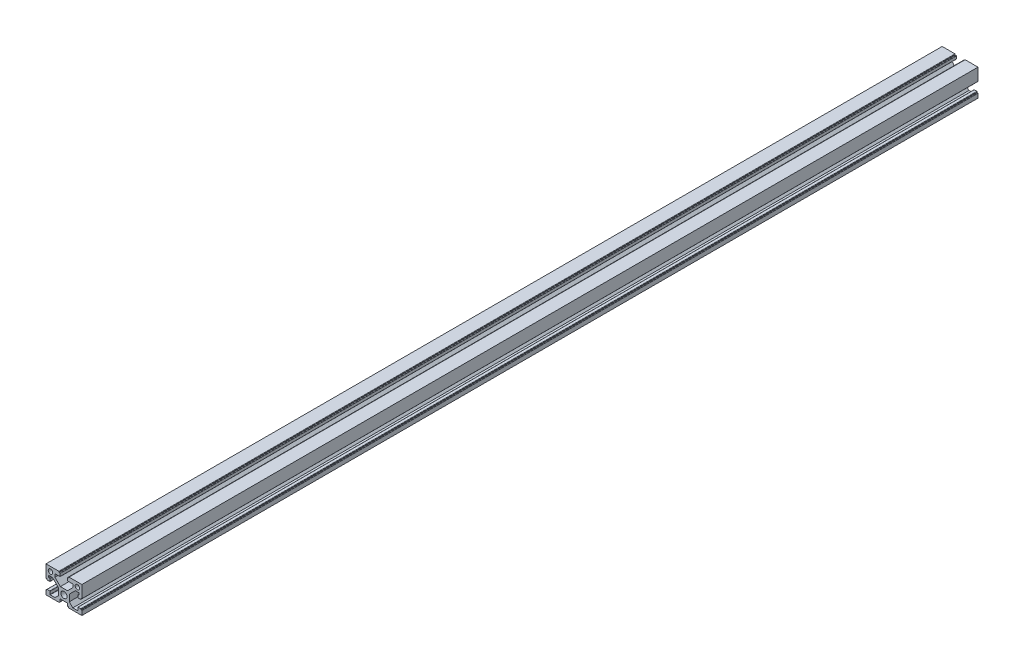
SolidWorks part; units mm, degrees
material "6063 T5"
ref_plane "Спереди" through (0, 0, 0) normal (0, 0, 1) x (1, 0, 0)
ref_plane "Сверху" through (0, 0, 0) normal (0, 1, 0) x (1, 0, 0)
ref_plane "Справа" through (0, 0, 0) normal (1, 0, 0) x (0, 0, -1)
sketch "Эскиз1" plane through (0, 0, 0) normal (0, 0, 1) x (1, 0, 0)
  line L0 (-20.0246, 21.0976) -> (19.9754, 21.0976) construction
  line L1 (-10, 20) -> (-20, 20)
  line L2 (-20, 20) -> (-20, 6.3)
  line L3 (-19.7, 6) -> (-19, 6)
  line L4 (-19, 6) -> (-19, 5.3)
  line L5 (-18.7, 5) -> (-15.8, 5)
  line L6 (-15.5, 5.3) -> (-15.5, 8)
  line L7 (-15.5, 8) -> (-16.7, 8)
  line L8 (-17, 8.3) -> (-17, 10.1)
  line L9 (-16.7, 10.4) -> (-12.7, 10.4)
  line L10 (-12.7, 10.4) -> (-6, 3.7)
  line L11 (-6, 3.7) -> (-6, -3.7)
  line L12 (-6, -3.7) -> (-9.9, -7.6)
  line L13 (-9.9, -7.6) -> (-15.2, -7.6)
  line L14 (-15.5, -7.3) -> (-15.5, -4.3)
  line L15 (-15.8, -4) -> (-18.7, -4)
  line L16 (-19, -4.3) -> (-19, -5)
  line L17 (-19, -5) -> (-19.7, -5)
  line L18 (-20, -5.3) -> (-20, -10)
  line L19 (-20, -10) -> (-5.4, -10)
  line L20 (-5.1, -9.7) -> (-5.1, -9)
  line L21 (-5.1, -9) -> (-4.4, -9)
  line L22 (-4.1, -8.7) -> (-4.1, -6)
  line L23 (-4.1, -6) -> (4.1, -6)
  line L24 (0, -6) -> (0, 0) construction
  line L25 (-15.5, 5) -> (-15.5, -4) construction
  line L26 (15.5, 5) -> (15.5, -4) construction
  line L27 (4.1, -8.7) -> (4.1, -6)
  line L28 (5.1, -9) -> (4.4, -9)
  line L29 (5.1, -9.7) -> (5.1, -9)
  line L30 (20, -10) -> (5.4, -10)
  line L31 (20, -5.3) -> (20, -10)
  line L32 (19, -5) -> (19.7, -5)
  line L33 (19, -4.3) -> (19, -5)
  line L34 (15.8, -4) -> (18.7, -4)
  line L35 (15.5, -7.3) -> (15.5, -4.3)
  line L36 (9.9, -7.6) -> (15.2, -7.6)
  line L37 (6, -3.7) -> (9.9, -7.6)
  line L38 (6, 3.7) -> (6, -3.7)
  line L39 (12.7, 10.4) -> (6, 3.7)
  line L40 (16.7, 10.4) -> (12.7, 10.4)
  line L41 (17, 8.3) -> (17, 10.1)
  line L42 (15.5, 8) -> (16.7, 8)
  line L43 (15.5, 5.3) -> (15.5, 8)
  line L44 (18.7, 5) -> (15.8, 5)
  line L45 (19, 6) -> (19, 5.3)
  line L46 (19.7, 6) -> (19, 6)
  line L47 (20, 20) -> (20, 6.3)
  line L48 (10, 20) -> (20, 20)
  line L49 (-15, 15) -> (15, 15) construction
  circle A0 centre (0, 0) radius 3.4
  arc A1 (-15.2, -7.6) -> (-15.5, -7.3) centre (-15.2, -7.3) cw
  arc A2 (-15.5, -4.3) -> (-15.8, -4) centre (-15.8, -4.3) ccw
  arc A3 (-18.7, -4) -> (-19, -4.3) centre (-18.7, -4.3) ccw
  arc A4 (-19.7, -5) -> (-20, -5.3) centre (-19.7, -5.3) ccw
  arc A5 (-20, 6.3) -> (-19.7, 6) centre (-19.7, 6.3) ccw
  arc A6 (-19, 5.3) -> (-18.7, 5) centre (-18.7, 5.3) ccw
  arc A7 (-15.8, 5) -> (-15.5, 5.3) centre (-15.8, 5.3) ccw
  arc A8 (-16.7, 8) -> (-17, 8.3) centre (-16.7, 8.3) cw
  arc A9 (-17, 10.1) -> (-16.7, 10.4) centre (-16.7, 10.1) cw
  arc A10 (17, 10.1) -> (16.7, 10.4) centre (16.7, 10.1) ccw
  arc A11 (16.7, 8) -> (17, 8.3) centre (16.7, 8.3) ccw
  arc A12 (15.8, 5) -> (15.5, 5.3) centre (15.8, 5.3) cw
  arc A13 (19, 5.3) -> (18.7, 5) centre (18.7, 5.3) cw
  arc A14 (20, 6.3) -> (19.7, 6) centre (19.7, 6.3) cw
  arc A15 (19.7, -5) -> (20, -5.3) centre (19.7, -5.3) cw
  arc A16 (18.7, -4) -> (19, -4.3) centre (18.7, -4.3) cw
  arc A17 (15.5, -4.3) -> (15.8, -4) centre (15.8, -4.3) cw
  arc A18 (15.2, -7.6) -> (15.5, -7.3) centre (15.2, -7.3) ccw
  arc A19 (5.1, -9.7) -> (5.4, -10) centre (5.4, -9.7) ccw
  arc A20 (4.1, -8.7) -> (4.4, -9) centre (4.4, -8.7) ccw
  arc A21 (-4.4, -9) -> (-4.1, -8.7) centre (-4.4, -8.7) ccw
  arc A22 (-5.4, -10) -> (-5.1, -9.7) centre (-5.4, -9.7) ccw
  circle A23 centre (15, 15) radius 2.5
  circle A24 centre (-15, 15) radius 2.5
  point P32 (0, 15)
  point P35 (-6, 0)
  point P45 (-20, -5)
  point P48 (-20, 6)
  point P57 (-17, 8)
  point P103 (17, 8)
  point P104 (20, 6)
  point P105 (20, -5)
  point P108 (5.1, -10)
  point P111 (4.1, -9)
  point P114 (-4.1, -9)
  point P117 (-5.1, -10)
  line B0 (10, 20) -> (5.7, 20)
  line B1 (5.4, 19.7) -> (5.4, 19)
  line B2 (5.4, 19) -> (4.4, 19)
  line B3 (4.1, 18.7) -> (4.1, 15.8)
  line B4 (4.4, 15.5) -> (9.7, 15.5)
  line B5 (10, 15.2) -> (10, 12)
  line B6 (10, 12) -> (4, 6)
  line B7 (0, 6) -> (0, 20) construction
  line B8 (-4, 6) -> (4, 6)
  line B9 (-10, 12) -> (-4, 6)
  line B10 (-10, 15.2) -> (-10, 12)
  line B11 (-4.4, 15.5) -> (-9.7, 15.5)
  line B12 (-4.1, 18.7) -> (-4.1, 15.8)
  line B13 (-5.4, 19) -> (-4.4, 19)
  line B14 (-5.4, 19.7) -> (-5.4, 19)
  line B15 (-10, 20) -> (-5.7, 20)
  arc B16 (9.7, 15.5) -> (10, 15.2) centre (9.7, 15.2) cw
  arc B17 (4.1, 15.8) -> (4.4, 15.5) centre (4.4, 15.8) ccw
  arc B18 (4.4, 19) -> (4.1, 18.7) centre (4.4, 18.7) ccw
  arc B19 (5.7, 20) -> (5.4, 19.7) centre (5.7, 19.7) ccw
  arc B20 (-5.7, 20) -> (-5.4, 19.7) centre (-5.7, 19.7) cw
  arc B21 (-4.4, 19) -> (-4.1, 18.7) centre (-4.4, 18.7) cw
  arc B22 (-4.1, 15.8) -> (-4.4, 15.5) centre (-4.4, 15.8) cw
  arc B23 (-9.7, 15.5) -> (-10, 15.2) centre (-9.7, 15.2) ccw
  line B24 (-10, 20) -> (-5.7, 20)
  line B25 (-5.4, 19.7) -> (-5.4, 19)
  line B26 (-5.4, 19) -> (-4.4, 19)
  line B27 (-4.1, 18.7) -> (-4.1, 15.8)
  line B28 (-4.4, 15.5) -> (-9.7, 15.5)
  line B29 (-10, 15.2) -> (-10, 12)
  line B30 (-10, 12) -> (-4, 6)
  line B31 (0, 6) -> (0, 20) construction
  line B32 (4, 6) -> (-4, 6)
  line B33 (10, 12) -> (4, 6)
  line B34 (10, 15.2) -> (10, 12)
  line B35 (4.4, 15.5) -> (9.7, 15.5)
  line B36 (4.1, 18.7) -> (4.1, 15.8)
  line B37 (5.4, 19) -> (4.4, 19)
  line B38 (5.4, 19.7) -> (5.4, 19)
  line B39 (10, 20) -> (5.7, 20)
  arc B40 (-9.7, 15.5) -> (-10, 15.2) centre (-9.7, 15.2) ccw
  arc B41 (-4.1, 15.8) -> (-4.4, 15.5) centre (-4.4, 15.8) cw
  arc B42 (-4.4, 19) -> (-4.1, 18.7) centre (-4.4, 18.7) cw
  arc B43 (-5.7, 20) -> (-5.4, 19.7) centre (-5.7, 19.7) cw
  arc B44 (5.7, 20) -> (5.4, 19.7) centre (5.7, 19.7) ccw
  arc B45 (4.4, 19) -> (4.1, 18.7) centre (4.4, 18.7) ccw
  arc B46 (4.1, 15.8) -> (4.4, 15.5) centre (4.4, 15.8) ccw
  arc B47 (9.7, 15.5) -> (10, 15.2) centre (9.7, 15.2) cw
  dimension "D8" = 7.4
  dimension "D11" = 9
  dimension "D1" = 6.8
  dimension "D23" = 0.3
  dimension "D24" = 0.3
  dimension "D25" = 5
  dimension "D2" = 20
  dimension "D3" = 40
  dimension "D4" = 1
  dimension "D5" = 4.5
  dimension "D6" = 14
  dimension "D7" = 7.3
  dimension "D9" = 135
  dimension "D10" = 135
  dimension "D12" = 18
  dimension "D13" = 1.5
  dimension "D14" = 11
  dimension "D15" = 10
  dimension "D16" = 30
  dimension "D17" = 6
  dimension "D18" = 3
  dimension "D19" = 1
  dimension "D20" = 8.2
  dimension "D21" = 10.2
  dimension "D22" = 3
  dimension "D26" = 30
  dimension "D27" = 25
sketch_block_instance "Блок1-2"
sketch_block "Блок1" parameters "D6"=0.3, "D9"=0.3, "D1"=20, "D2"=4.5, "D3"=8, "D4"=45, "D5"=10.8, "D7"=8.2, "D8"=14
sketch_block_instance "Блок1-6"
extrude "Бобышка-Вытянуть1" add sketch "Эскиз1" along normal blind 1000 contours B23 B11 B22 B12 B21 B13 B14 B20 B15 L1 L2 A5 L3 L4 A6 L5 A7 L6 L7 A8 L8 A9 L9 L10 L11 L12 L13 A1 L14 A2 L15 A3 L16 L17 A4 L18 L19 A22 L20 L21 A21 L22 L23 L27 A20 L28 L29 A19 L30 L31 A15
